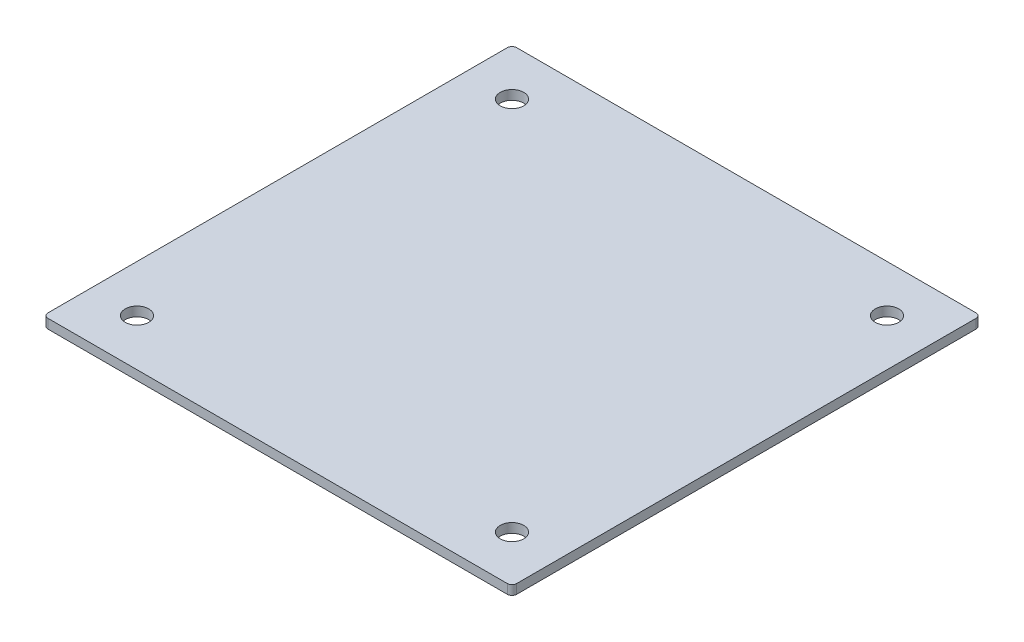
SolidWorks part; units mm, degrees
ref_plane "Front Plane" through (0, 0, 0) normal (0, 0, 1) x (1, 0, 0)
ref_plane "Top Plane" through (0, 0, 0) normal (0, 1, 0) x (1, 0, 0)
ref_plane "Right Plane" through (0, 0, 0) normal (1, 0, 0) x (0, 0, -1)
sketch "Sketch1" plane through (0, 0, 0) normal (0, 1, 0) x (1, 0, 0)
  line L1 (-98, -100) -> (98, -100)
  line L2 (-100, -98) -> (-100, 98)
  line L3 (-98, 100) -> (98, 100)
  line L4 (100, -98) -> (100, 98)
  line L5 (-100, -100) -> (100, 100) construction
  line L6 (-100, 100) -> (100, -100) construction
  circle A0 centre (-80, -80) radius 5
  circle A1 centre (80, -80) radius 5
  circle A2 centre (80, 80) radius 5
  circle A3 centre (-80, 80) radius 5
  arc A4 (-100, -98) -> (-98, -100) centre (-98, -98) ccw
  arc A5 (98, -100) -> (100, -98) centre (98, -98) ccw
  arc A6 (100, 98) -> (98, 100) centre (98, 98) ccw
  arc A7 (-100, 98) -> (-98, 100) centre (-98, 98) cw
  point P0 (0, 0)
  dimension "D3" = 10
  dimension "D8" = 2
  dimension "D1" = 200
  dimension "D2" = 200
  dimension "D4" = 20
  dimension "D5" = 20
  dimension "D6" = 2
  dimension "D7" = 2
extrude "Boss-Extrude1" add sketch "Sketch1" along normal blind 4
